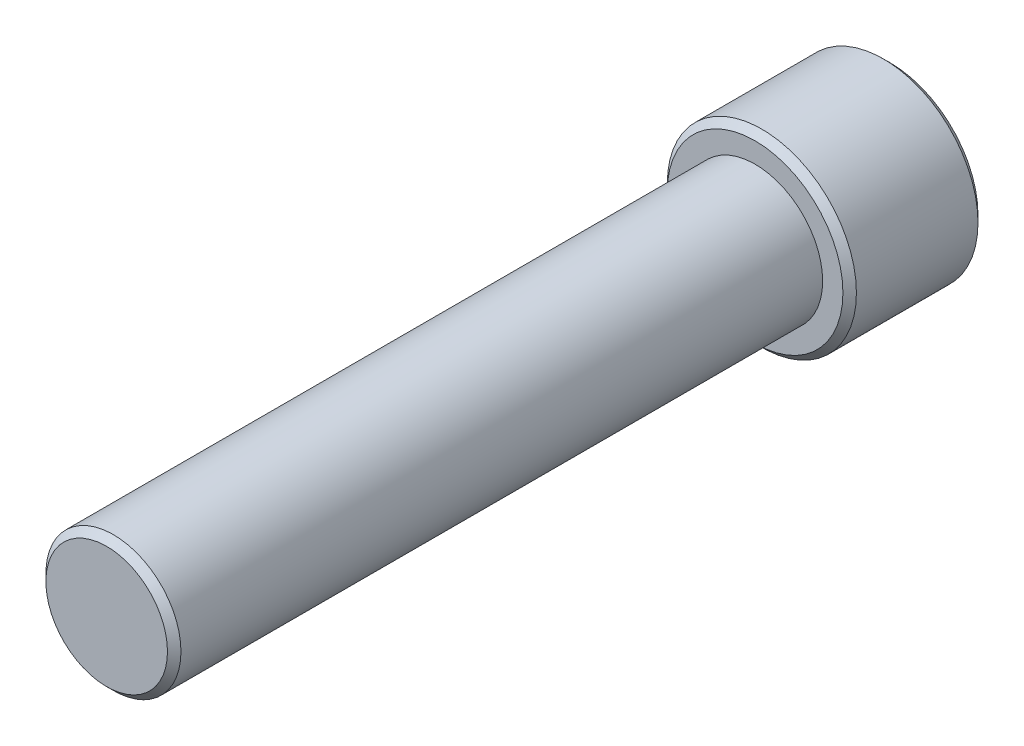
SolidWorks part; units mm, degrees
ref_plane "Piano frontale" through (0, 0, 0) normal (0, 0, 1) x (1, 0, 0)
ref_plane "Piano superiore" through (0, 0, 0) normal (0, 1, 0) x (1, 0, 0)
ref_plane "Piano destro" through (0, 0, 0) normal (1, 0, 0) x (0, 0, -1)
sketch "Schizzo1" plane through (0, 0, 0) normal (0, 0, 1) x (1, 0, 0)
  circle A0 centre (0, 0) radius 3.5
  dimension "D1" = 7
extrude "Estrusione-Estrusione1" add sketch "Schizzo1" along normal blind 5
sketch "Schizzo2" plane through (0, 0, 5) normal (0, 0, 1) x (1, 0, 0)
  circle A0 centre (0, 0) radius 2.5
  dimension "D1" = 5
extrude "Estrusione-Estrusione2" add sketch "Schizzo2" along normal blind 24
chamfer "Smusso1" distance 0.25 angle 45 3 edges at (3.5, 0, 0) (3.5, 0, 5) (2.5, 0, 29)
